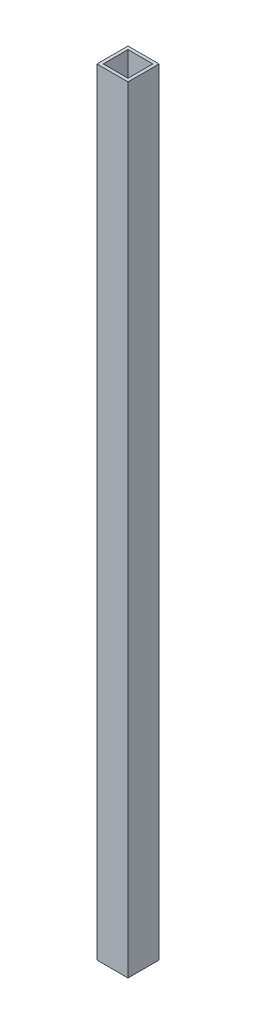
SolidWorks part; units mm, degrees
ref_plane "Спереди" through (0, 0, 0) normal (0, 0, 1) x (1, 0, 0)
ref_plane "Сверху" through (0, 0, 0) normal (0, 1, 0) x (1, 0, 0)
ref_plane "Справа" through (0, 0, 0) normal (1, 0, 0) x (0, 0, -1)
sketch "Эскиз1" plane through (0, 0, 0) normal (0, 1, 0) x (1, 0, 0)
  line L1 (5, -5) -> (-5, -5)
  line L2 (5, -5) -> (5, 5)
  line L3 (5, 5) -> (-5, 5)
  line L4 (-5, -5) -> (-5, 5)
  line L5 (5, -5) -> (-5, 5) construction
  line L6 (5, 5) -> (-5, -5) construction
  line L7 (4, -4) -> (-4, -4)
  line L8 (4, -4) -> (4, 4)
  line L9 (4, 4) -> (-4, 4)
  line L10 (-4, -4) -> (-4, 4)
  line L11 (4, -4) -> (-4, 4) construction
  line L12 (4, 4) -> (-4, -4) construction
  point P0 (0, 0)
  point P7 (0, 0)
  dimension "D1" = 10
  dimension "D2" = 10
  dimension "D3" = 8
  dimension "D4" = 8
extrude "Бобышка-Вытянуть1" add sketch "Эскиз1" along normal blind 250
